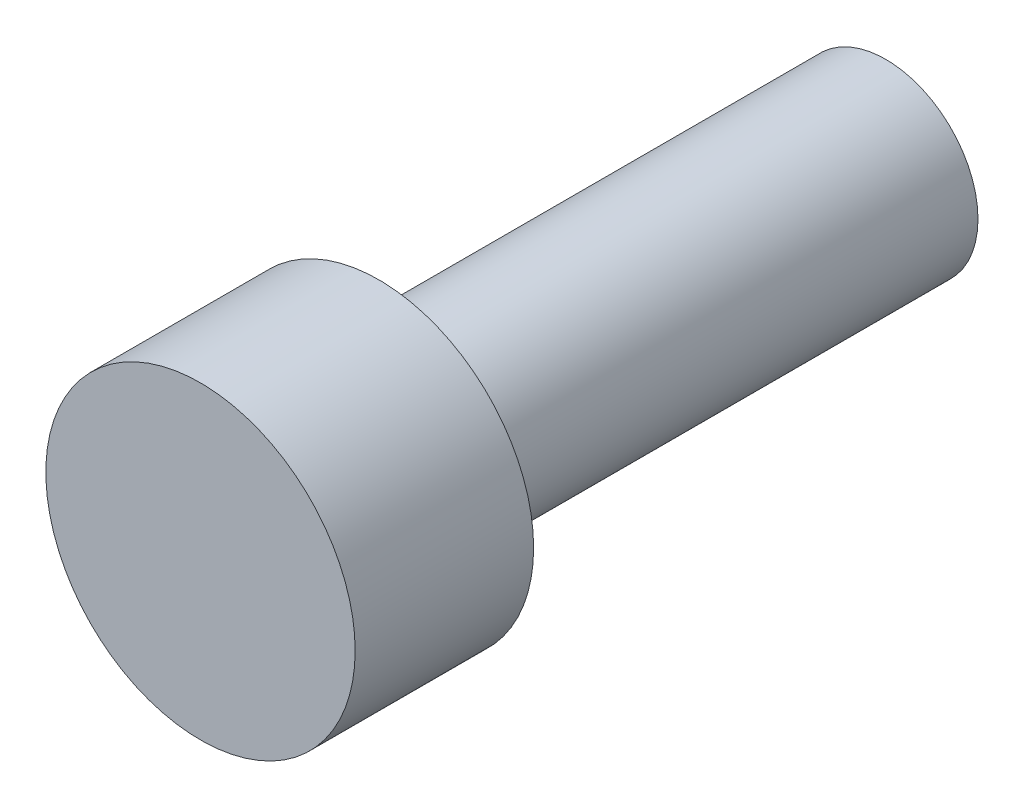
SolidWorks part; units mm, degrees
ref_plane "Front Plane" through (0, 0, 0) normal (0, 0, 1) x (1, 0, 0)
ref_plane "Top Plane" through (0, 0, 0) normal (0, 1, 0) x (1, 0, 0)
ref_plane "Right Plane" through (0, 0, 0) normal (1, 0, 0) x (0, 0, -1)
sketch "Sketch1" plane through (0, 0, 0) normal (0, 0, 1) x (1, 0, 0)
  circle A0 centre (0, 0) radius 6.5
  dimension "D1" = 13
extrude "Boss-Extrude1" add sketch "Sketch1" along normal blind 7.5
sketch "Sketch2" plane through (0, 0, 0) normal (0, 0, -1) x (-1, 0, 0)
  circle A0 centre (0, 0) radius 3.875
  dimension "D1" = 7.75
extrude "Boss-Extrude2" add sketch "Sketch2" along normal blind 21.3
